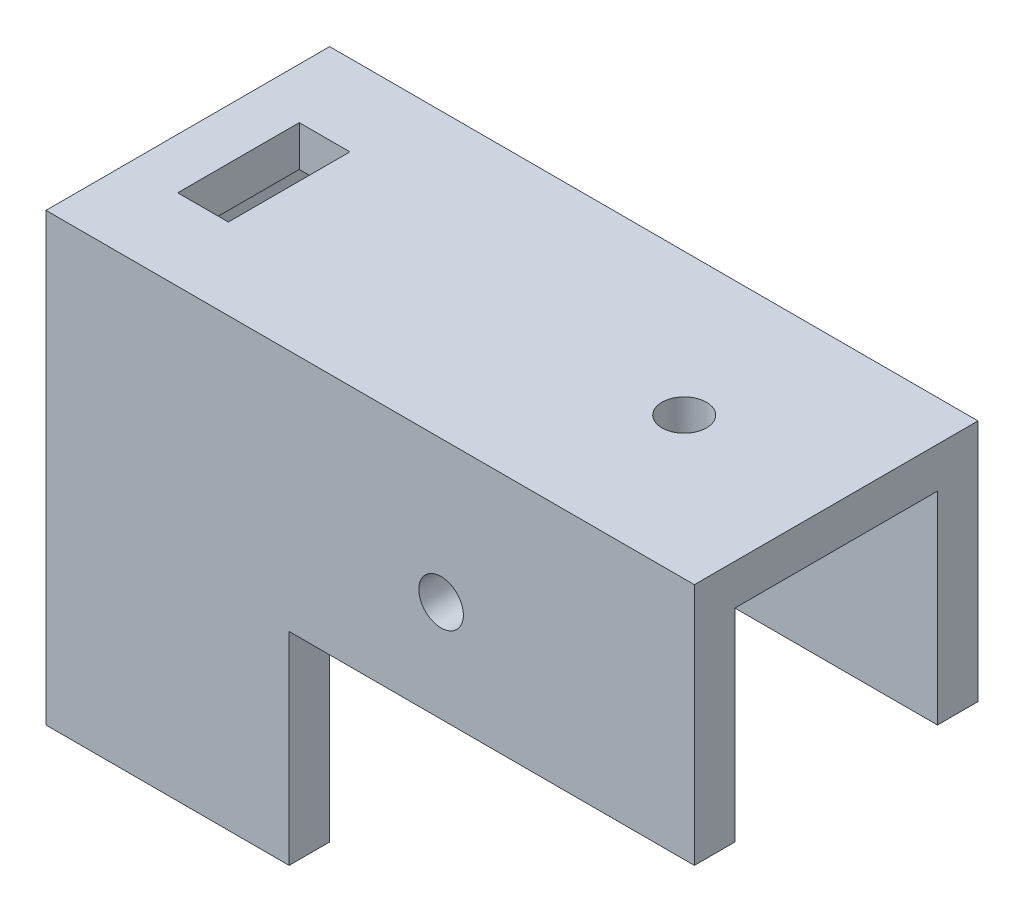
SolidWorks part; units mm, degrees
ref_plane "Plan de face" through (0, 0, 0) normal (0, 0, 1) x (1, 0, 0)
ref_plane "Plan de dessus" through (0, 0, 0) normal (0, 1, 0) x (1, 0, 0)
ref_plane "Plan de droite" through (0, 0, 0) normal (1, 0, 0) x (0, 0, -1)
sketch "Esquisse1" plane through (0, 0, 0) normal (0, 0, 1) x (1, 0, 0)
  line L0 (0, 0) -> (64, 0)
  line L1 (64, 0) -> (64, -24)
  line L2 (64, -24) -> (24, -24)
  line L3 (24, -24) -> (24, -44)
  line L4 (24, -44) -> (0, -44)
  line L5 (0, -44) -> (0, 0)
  dimension "D1" = 64
  dimension "D2" = 24
  dimension "D3" = 24
  dimension "D4" = 44
extrude "Boss.-Extru.1" add sketch "Esquisse1" along normal blind 28
sketch "Esquisse2" plane through (0, -44, 0) normal (0, -1, 0) x (1, 0, 0)
  line L0 (24, 24) -> (17, 24)
  line L1 (24, 28) -> (24, 0) construction
  line L2 (17, 24) -> (17, 21.5)
  line L3 (17, 21.5) -> (11, 21.5)
  line L4 (11, 21.5) -> (11, 24)
  line L5 (11, 24) -> (4, 24)
  line L6 (4, 24) -> (4, 4)
  line L7 (4, 4) -> (11, 4)
  line L8 (11, 4) -> (11, 6.5)
  line L9 (11, 6.5) -> (17, 6.5)
  line L10 (17, 6.5) -> (17, 4)
  line L11 (17, 4) -> (24, 4)
  line L12 (24, 4) -> (24, 24)
  line L13 (0, 0) -> (24, 0) construction
  line L14 (0, 28) -> (24, 28) construction
  line L15 (0, 28) -> (0, 0) construction
  dimension "D1" = 2.5
  dimension "D2" = 6
  dimension "D3" = 2.5
  dimension "D4" = 7
  dimension "D5" = 20
  dimension "D6" = 7
  dimension "D7" = 2.5
  dimension "D8" = 6
  dimension "D9" = 2.5
  dimension "D10" = 7
  dimension "D11" = 4
  dimension "D12" = 4
  dimension "D13" = 4
extrude "Enlèv. mat.-Extru.1" cut sketch "Esquisse2" against normal offset from surface (40 mm away) 4
sketch "Esquisse3" plane through (0, -24, 0) normal (0, -1, 0) x (1, 0, 0)
  line L0 (64, 28) -> (64, 0) construction
  line L1 (64, 24) -> (31, 24)
  line L2 (64, 24) -> (64, 4)
  line L3 (64, 4) -> (31, 4)
  line L4 (31, 24) -> (31, 4)
  line L5 (24, 24) -> (24, 4) construction
  line L6 (24, 28) -> (64, 28) construction
  line L7 (24, 0) -> (64, 0) construction
  dimension "D1" = 7
  dimension "D2" = 4
  dimension "D3" = 4
extrude "Enlèv. mat.-Extru.2" cut sketch "Esquisse3" against normal offset from surface (20 mm away) 4
hole_wizard "Dégagement M41" positions "Esquisse6" profile "Esquisse4" hole size "M4" standard "Din"
sketch "Esquisse6" plane through (0, 0, 0) normal (-1, 0, 0) x (0, 0, 1)
  line L0 (14, 0) -> (14, -44) construction
  line L1 (28, 0) -> (0, 0) construction
  line L2 (28, -44) -> (0, -44) construction
  point P9 (14, -15.5)
  point P10 (14, -30.5)
  dimension "D1" = 15.5
  dimension "D2" = 13.5
sketch "Esquisse4" plane through (0, -15.5, 14) normal (0, 1, 0) x (0, 0, 1)
  line L0 (0, 0) -> (0, 5)
  line L1 (0, 5) -> (2.2, 5)
  line L2 (2.2, 5) -> (2.2, 0)
  line L5 (2.2, 0) -> (0, 0)
  line L10 (0, 5) -> (-2.2, 5) construction
  line L11 (0, -6.35) -> (0, 107.95) construction
  dimension "Diamètre du perçage" = 4.4
  dimension "Profondeur du perçage" = 5
  dimension "Angle de pointe" = 180
hole_wizard "Dégagement M42" positions "Esquisse8" profile "Esquisse9" hole size "M4" standard "Din" end condition through all
sketch "Esquisse8" plane through (0, 0, 28) normal (0, 0, 1) x (1, 0, 0)
  line L0 (64, -24) -> (64, 0) construction
  line L1 (24, -24) -> (64, -24) construction
  point P0 (39, -14)
  dimension "D1" = 25
  dimension "D2" = 10
sketch "Esquisse9" plane through (39, -14, 28) normal (1, 0, 0) x (0, -1, 0)
  line L0 (0, 0) -> (0, 28)
  line L1 (0, 28) -> (2.2, 28)
  line L2 (2.2, 28) -> (2.2, 0)
  line L5 (2.2, 0) -> (0, 0)
  line L11 (0, -6.35) -> (0, 107.95) construction
  dimension "Diamètre du perçage jusqu'au prochain" = 4.4
  dimension "Profondeur du perçage jusqu'au prochain" = 28
hole_wizard "Dégagement M43" positions "Esquisse11" profile "Esquisse10" hole size "M4" standard "Din"
sketch "Esquisse11" plane through (0, 0, 0) normal (0, 1, 0) x (1, 0, 0)
  line L0 (64, -14) -> (0, -14) construction
  line L1 (64, -28) -> (64, 0) construction
  line L2 (0, -28) -> (0, 0) construction
  point P0 (49, -14)
  dimension "D1" = 15
sketch "Esquisse10" plane through (49, 0, 14) normal (1, 0, 0) x (0, 0, 1)
  line L0 (0, 0) -> (0, 5)
  line L1 (0, 5) -> (2.2, 5)
  line L2 (2.2, 5) -> (2.2, 0)
  line L5 (2.2, 0) -> (0, 0)
  line L10 (0, 5) -> (-2.2, 5) construction
  line L11 (0, -6.35) -> (0, 107.95) construction
  dimension "Diamètre du perçage" = 4.4
  dimension "Profondeur du perçage" = 5
  dimension "Angle de pointe" = 180
sketch "Esquisse12" plane through (0, 0, 0) normal (-1, 0, 0) x (0, 0, 1)
  line L0 (28, -44) -> (0, -44) construction
  line L1 (18, -34) -> (10, -34)
  line L2 (18, -34) -> (18, -38)
  line L3 (18, -38) -> (10, -38)
  line L4 (10, -34) -> (10, -38)
  line L5 (14, -38) -> (14, -44) construction
  dimension "D1" = 8
  dimension "D2" = 6
  dimension "D3" = 4
sketch "Esquisse13" plane through (0, 0, 0) normal (0, 1, 0) x (1, 0, 0)
  line L0 (0, -28) -> (0, 0) construction
  line L1 (10, -8) -> (5, -8)
  line L2 (10, -8) -> (10, -20)
  line L3 (10, -20) -> (5, -20)
  line L4 (5, -8) -> (5, -20)
  line L5 (5, -14) -> (0, -14) construction
  dimension "D1" = 12
  dimension "D2" = 5
  dimension "D3" = 5
extrude "Enlèv. mat.-Extru.4" cut sketch "Esquisse13" against normal blind 10
